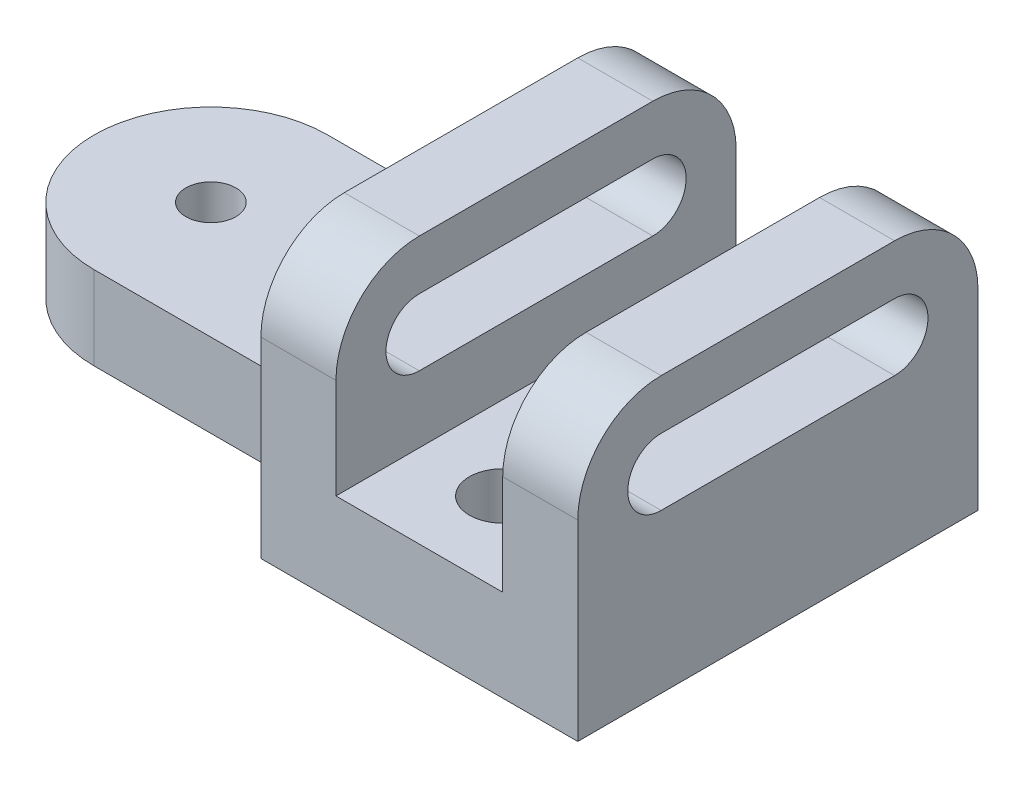
SolidWorks part; units mm, degrees
ref_plane "Front Plane" through (0, 0, 0) normal (0, 0, 1) x (1, 0, 0)
ref_plane "Top Plane" through (0, 0, 0) normal (0, 1, 0) x (1, 0, 0)
ref_plane "Right Plane" through (0, 0, 0) normal (1, 0, 0) x (0, 0, -1)
sketch "Sketch1" plane through (0, 0, 0) normal (1, 0, 0) x (0, 0, -1)
  line L0 (-60.325, 52.3875) -> (-15.875, 52.3875)
  line L1 (0, 36.5125) -> (0, 0)
  line L2 (-76.2, 36.5125) -> (-76.2, 0)
  line L3 (-76.2, 0) -> (0, 0)
  line L5 (-60.325, 42.8625) -> (-15.875, 42.8625)
  line L7 (-60.325, 30.1625) -> (-15.875, 30.1625)
  line L9 (-38.1, 0) -> (-38.1, 42.8625) construction
  arc A0 (-60.325, 42.8625) -> (-60.325, 30.1625) centre (-60.325, 36.5125) ccw
  arc A1 (-60.325, 52.3875) -> (-76.2, 36.5125) centre (-60.325, 36.5125) ccw
  arc A2 (-15.875, 52.3875) -> (0, 36.5125) centre (-15.875, 36.5125) cw
  arc A3 (-15.875, 42.8625) -> (-15.875, 30.1625) centre (-15.875, 36.5125) cw
  point P8 (-38.1, 52.3875)
  point P10 (-38.1, 30.1625)
  dimension "D5" = 6.35
  dimension "D6" = 31.75
  dimension "D1" = 38.1
  dimension "D2" = 36.5125
  dimension "D3" = 12.7
  dimension "D4" = 22.225
  dimension "D7" = 36.5125
extrude "Boss-Extrude1" add sketch "Sketch1" along normal blind 60.325
sketch "Sketch5" plane through (0, 0, 76.2) normal (0, 0, 1) x (1, 0, 0)
  line L0 (60.325, 52.3875) -> (0, 52.3875) construction
  line L1 (14.2875, 52.3875) -> (46.0375, 52.3875)
  line L2 (14.2875, 52.3875) -> (14.2875, 17.4625)
  line L3 (14.2875, 17.4625) -> (46.0375, 17.4625)
  line L4 (46.0375, 52.3875) -> (46.0375, 17.4625)
  line L5 (60.325, 0) -> (0, 0) construction
  point P6 (30.1625, 52.3875)
  point P7 (30.1625, 52.3875)
  dimension "D1" = 17.4625
  dimension "D2" = 31.75
extrude "Cut-Extrude1" cut sketch "Sketch5" against normal through all
sketch "Sketch6" plane through (0, 0, 0) normal (0, -1, 0) x (1, 0, 0)
  line L0 (0, 76.2) -> (0, 0) construction
  line L1 (0, 60.325) -> (-47.625, 60.325)
  line L2 (0, 60.325) -> (0, 15.875)
  line L3 (0, 15.875) -> (-47.625, 15.875)
  line L4 (-47.625, 60.325) -> (-47.625, 15.875)
  circle A0 centre (-47.625, 38.1) radius 22.225
  circle A1 centre (-47.625, 38.1) radius 4.7625
  point P6 (0, 38.1)
  point P7 (0, 38.1)
  line M2 (0, 76.2) -> (0, 0)
  dimension "D3" = 9.525
  dimension "D1" = 22.225
  dimension "D2" = 47.625
extrude "Boss-Extrude2" add sketch "Sketch6" against normal blind 15.875 contours A0 L3 L1 M2 | A1 L4 A0 | A1 L4 A0
fillet "Fillet1" radius 12.7 2 edges
sketch "Sketch7" plane through (0, 17.4625, 0) normal (0, 1, 0) x (1, 0, 0)
  line L0 (30.1625, 0) -> (30.1625, -76.2) construction
  line L1 (14.2875, 0) -> (46.0375, 0) construction
  line L2 (14.2875, -76.2) -> (46.0375, -76.2) construction
  line L3 (30.1625, -15.875) -> (30.1625, -60.325)
  circle A0 centre (30.1625, -15.875) radius 6.35
  circle A1 centre (30.1625, -60.325) radius 6.35
  point P10 (30.1625, -38.1)
  point P12 (30.1625, -38.1)
  dimension "D2" = 12.7
  dimension "D3" = 12.7
  dimension "D1" = 44.45
extrude "Cut-Extrude2" cut sketch "Sketch7" against normal through all contours A0 L0 L3 | L3 L0 A1 | L0 L3 A1
